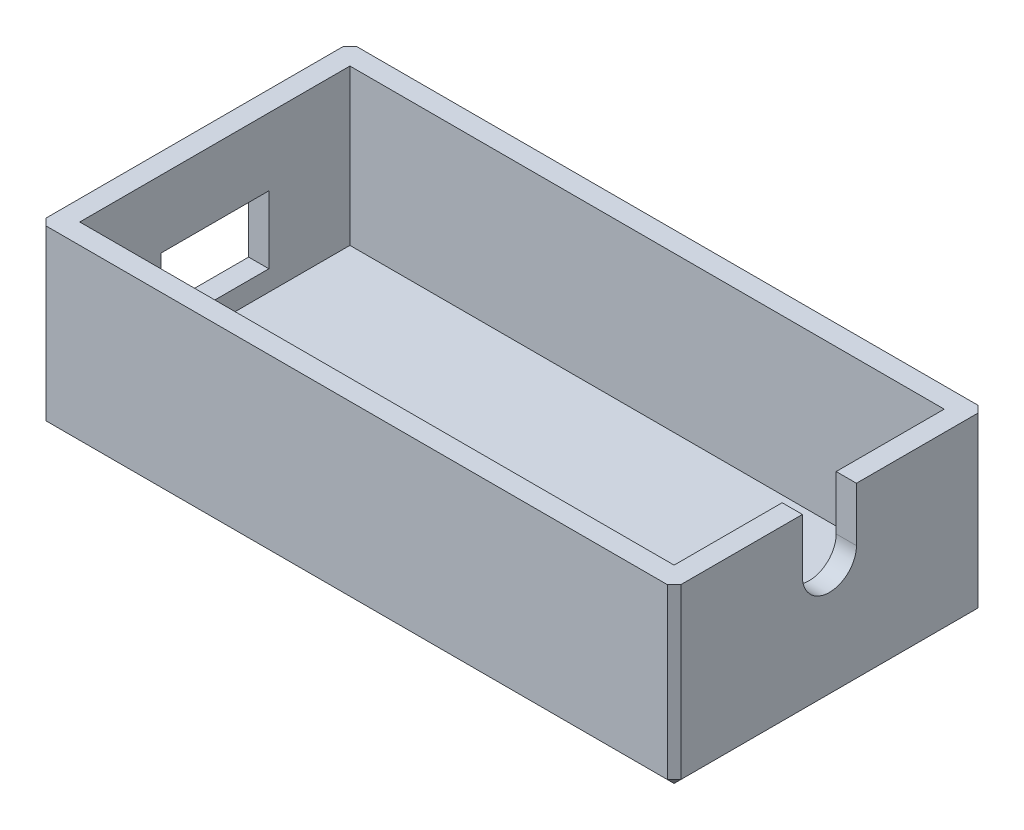
SolidWorks part; units mm, degrees
ref_plane "Front Plane" through (0, 0, 0) normal (0, 0, 1) x (1, 0, 0)
ref_plane "Top Plane" through (0, 0, 0) normal (0, 1, 0) x (1, 0, 0)
ref_plane "Right Plane" through (0, 0, 0) normal (1, 0, 0) x (0, 0, -1)
sketch "Sketch1" plane through (0, 0, 0) normal (0, 1, 0) x (1, 0, 0)
  line L1 (-21.5, 6.7089) -> (22.5, 6.7089)
  line L2 (-21.5, 6.7089) -> (-21.5, -13.2911)
  line L3 (-21.5, -13.2911) -> (22.5, -13.2911)
  line L4 (22.5, 6.7089) -> (22.5, -13.2911)
  line L5 (-23, 8.2089) -> (24, 8.2089)
  line L6 (-23, 8.2089) -> (-23, -14.7911)
  line L7 (-23, -14.7911) -> (24, -14.7911)
  line L8 (24, 8.2089) -> (24, -14.7911)
  dimension "D1" = 44
  dimension "D2" = 20
  dimension "D3" = 1.5
  dimension "D4" = 1.5
  dimension "D5" = 1.5
  dimension "D6" = 1.5
extrude "Boss-Extrude1" add sketch "Sketch1" along normal blind 13 contours L4 L1 L2 L3 | L8 L5 L6 L7 L1 L4 L3 L2
sketch "Sketch2" plane through (0, 13, 0) normal (0, 1, 0) x (1, 0, 0)
  line L0 (-23, 8.2089) -> (24, 8.2089) construction
  line L1 (-21.5, 6.7089) -> (22.5, 6.7089)
  line L2 (-21.5, 6.7089) -> (-21.5, -13.2911)
  line L3 (-21.5, -13.2911) -> (22.5, -13.2911)
  line L4 (22.5, 6.7089) -> (22.5, -13.2911)
  line L5 (-23, 8.2089) -> (-23, -14.7911) construction
  line L6 (24, 8.2089) -> (24, -14.7911) construction
  line L7 (-23, -14.7911) -> (24, -14.7911) construction
  dimension "D1" = 1.5
  dimension "D2" = 1.5
  dimension "D3" = 1.5
  dimension "D4" = 1.5
extrude "Cut-Extrude1" cut sketch "Sketch2" against normal blind 11.5
sketch "Sketch3" plane through (-21.5, 0, 0) normal (1, 0, 0) x (0, 0, -1)
  line L0 (12.65, 0) -> (-12.65, 0) construction
  line L1 (-7.2911, 8) -> (0.7089, 8)
  line L2 (-7.2911, 8) -> (-7.2911, 3)
  line L3 (-7.2911, 3) -> (0.7089, 3)
  line L4 (0.7089, 8) -> (0.7089, 3)
  line L5 (6.7089, 1.5) -> (-13.2911, 1.5) construction
  point P6 (-3.2911, 3)
  point P9 (-3.2911, 1.5)
  dimension "D1" = 3
  dimension "D2" = 8
  dimension "D3" = 8
  dimension "D4" = 0
extrude "Cut-Extrude2" cut sketch "Sketch3" against normal blind 11.5
sketch "Sketch4" plane through (22.5, 0, 0) normal (-1, 0, 0) x (0, 0, 1)
  line L0 (13.2911, 13) -> (-6.7089, 13) construction
  line L2 (1.2911, 13) -> (5.2911, 13)
  line L3 (1.2911, 13) -> (1.2911, 9)
  line L4 (1.2911, 9) -> (5.2911, 9)
  line L5 (5.2911, 13) -> (5.2911, 9)
  circle A0 centre (3.2911, 9) radius 2
  point P4 (3.2911, 13)
  line M3 (13.2911, 13) -> (-6.7089, 13)
  dimension "D1" = 4
  dimension "D2" = 4
  dimension "D3" = 0
  dimension "D4" = 2
  dimension "D5" = 2
extrude "Cut-Extrude3" cut sketch "Sketch4" against normal blind 11.5 contours L4 A0 | L4 A0 | A0 L5 L3 M3
chamfer "Chamfer1" distance 0.5 angle 45 8 edges at (-23, 6.5, -8.2089) (-23, 6.5, 14.7911) (24, 6.5, 14.7911) (24, 6.5, -8.2089) (24, 0, 3.2911) (0.5, 0, -8.2089) (-23, 0, 3.2911) (0.5, 0, 14.7911)
